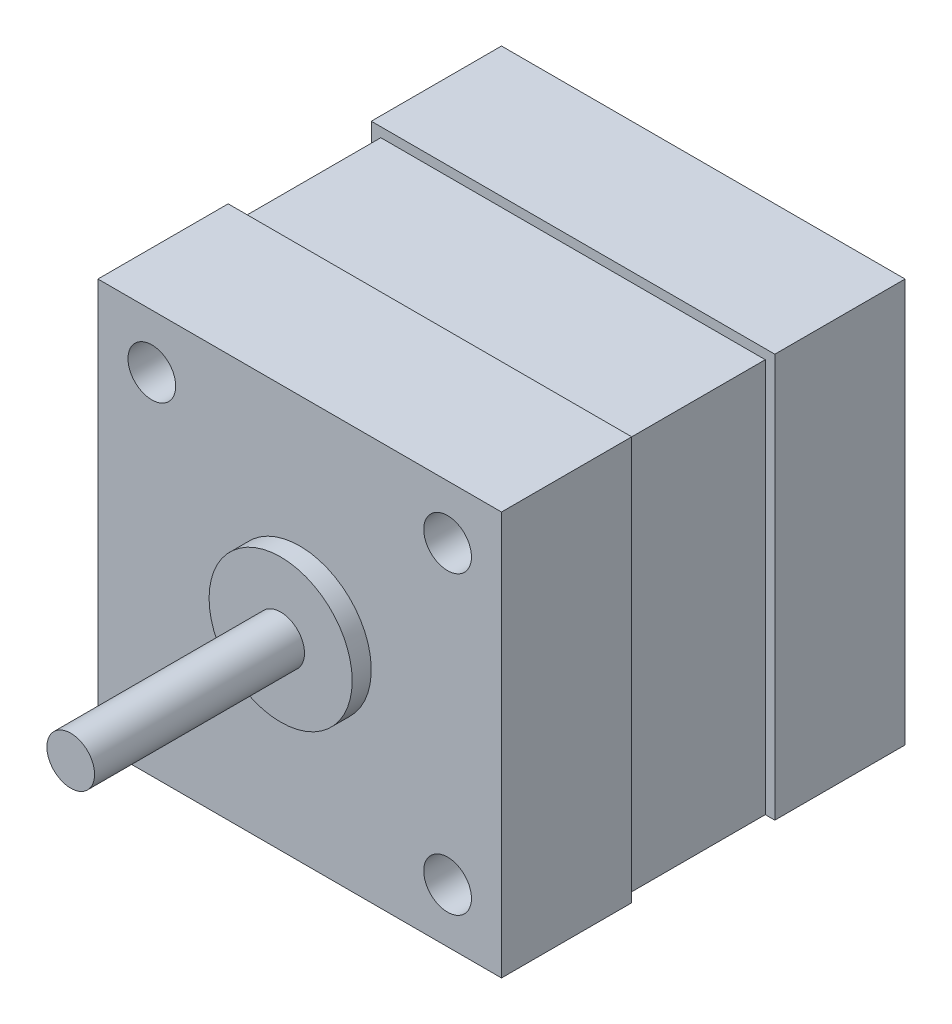
SolidWorks part; units mm, degrees
ref_plane "Front Plane" through (0, 0, 0) normal (0, 0, 1) x (1, 0, 0)
ref_plane "Top Plane" through (0, 0, 0) normal (0, 1, 0) x (1, 0, 0)
ref_plane "Right Plane" through (0, 0, 0) normal (1, 0, 0) x (0, 0, -1)
sketch "Sketch1" plane through (0, 0, 0) normal (0, 0, 1) x (1, 0, 0)
  line L1 (-21.15, -21.15) -> (21.15, -21.15)
  line L2 (-21.15, -21.15) -> (-21.15, 21.15)
  line L3 (-21.15, 21.15) -> (21.15, 21.15)
  line L4 (21.15, -21.15) -> (21.15, 21.15)
  line L5 (-21.15, -21.15) -> (21.15, 21.15) construction
  line L6 (-21.15, 21.15) -> (21.15, -21.15) construction
  circle A0 centre (-15.5, 15.5) radius 2.5
  circle A1 centre (15.5, 15.5) radius 2.5
  circle A2 centre (15.5, -15.5) radius 2.5
  circle A3 centre (-15.5, -15.5) radius 2.5
  point P0 (0, 0)
  dimension "D4" = 5
  dimension "D1" = 42.3
  dimension "D2" = 42.3
  dimension "D3" = 15.5
  dimension "D5" = 2
  dimension "D6" = 2
extrude "Boss-Extrude1" add sketch "Sketch1" along normal blind 42.3
sketch "Sketch2" plane through (0, 0, 42.3) normal (0, 0, 1) x (1, 0, 0)
  circle A0 centre (0, 0) radius 2.5
  dimension "D1" = 5
extrude "Boss-Extrude2" add sketch "Sketch2" along normal blind 24
sketch "Sketch3" plane through (0, 0, 42.3) normal (0, 0, 1) x (1, 0, 0)
  circle A0 centre (0, 0) radius 7.5
  dimension "D1" = 15
extrude "Boss-Extrude3" add sketch "Sketch3" along normal blind 2
sketch "Sketch4" plane through (21.15, 0, 0) normal (1, 0, 0) x (0, 0, -1)
  line L0 (-21.15, 21.15) -> (-21.15, -21.15) construction
  line L1 (-42.3, 21.15) -> (0, 21.15) construction
  line L2 (-42.3, -21.15) -> (0, -21.15) construction
  line L4 (-28.65, -21.15) -> (-13.65, -21.15)
  line L5 (-28.65, -21.15) -> (-28.65, 21.15)
  line L6 (-28.65, 21.15) -> (-13.65, 21.15)
  line L7 (-13.65, -21.15) -> (-13.65, 21.15)
  line L8 (-28.65, -21.15) -> (-13.65, 21.15) construction
  line L9 (-28.65, 21.15) -> (-13.65, -21.15) construction
  point P6 (-21.15, 0)
  dimension "D1" = 15
extrude "Cut-Extrude1" cut sketch "Sketch4" against normal blind 1
sketch "Sketch5" plane through (0, 21.15, 0) normal (0, 1, 0) x (1, 0, 0)
  line L0 (20.15, -21.15) -> (-21.15, -21.15) construction
  line L1 (20.15, -13.65) -> (20.15, -28.65) construction
  line L2 (-21.15, -42.3) -> (-21.15, 0) construction
  line L4 (-21.15, -13.65) -> (20.15, -13.65)
  line L5 (-21.15, -13.65) -> (-21.15, -28.65)
  line L6 (-21.15, -28.65) -> (20.15, -28.65)
  line L7 (20.15, -13.65) -> (20.15, -28.65)
  line L8 (-21.15, -13.65) -> (20.15, -28.65) construction
  line L9 (-21.15, -28.65) -> (20.15, -13.65) construction
  point P6 (-0.5, -21.15)
extrude "Cut-Extrude2" cut sketch "Sketch5" against normal blind 1
mirror "Mirror1" about plane through (0, 0, 0) normal (1, 0, 0) of "Cut-Extrude1"
